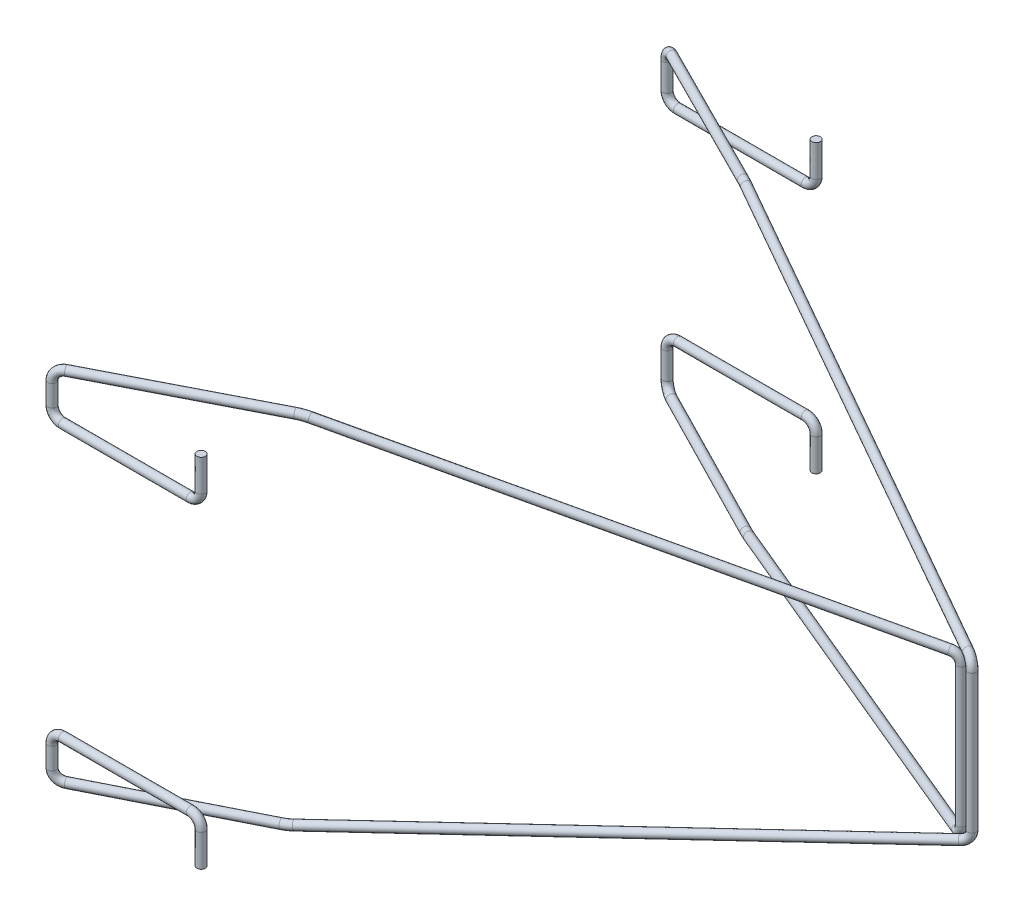
SolidWorks part; units mm, degrees
ref_plane "Front" through (0, 0, 0) normal (0, 0, 1) x (1, 0, 0)
ref_plane "Top" through (0, 0, 0) normal (0, 1, 0) x (1, 0, 0)
ref_plane "Right" through (0, 0, 0) normal (1, 0, 0) x (0, 0, -1)
sketch "Sketch1" plane through (0, 0, 0) normal (1, 0, 0) x (0, 0, -1)
  line L0 (105.8477, -16.8339) -> (302.3227, -5.6613)
  line L1 (0, 17) -> (100, 17)
  line L2 (0, 17) -> (0, -17)
  line L3 (0, -17) -> (100, -17)
  line L4 (105.8477, 16.8339) -> (302.3227, 5.6613)
  line L5 (308, 5.5) -> (360, 5.5)
  line L6 (308, -5.5) -> (360, -5.5)
  line L7 (360, -5.5) -> (360, 5.5)
  line L8 (360, 0) -> (0, 0) construction
  line L9 (116.1325, 16.249) -> (116.1325, -16.249) construction
  line L10 (173.8675, 12.9659) -> (173.8675, -12.9659) construction
  line L11 (145, 14.6075) -> (145, -14.6075) construction
  line L12 (145, 0) -> (173.8675, -50) construction
  line L13 (145, 0) -> (116.1325, -50) construction
  line L14 (116.1325, -50) -> (173.8675, -50) construction
  line L15 (145, -50) -> (145, -14.6075) construction
  arc A0 (100, 17) -> (105.8477, 16.8339) centre (100, -86) cw
  arc A1 (100, -17) -> (105.8477, -16.8339) centre (100, 86) ccw
  arc A2 (302.3227, 5.6613) -> (308, 5.5) centre (308, 105.5) ccw
  arc A3 (302.3227, -5.6613) -> (308, -5.5) centre (308, -105.5) cw
  dimension "D5" = 103
  dimension "D6" = 100
  dimension "D1" = 11
  dimension "D2" = 34
  dimension "D3" = 100
  dimension "D4" = 360
  dimension "D7" = 52
  dimension "D8" = 145
  dimension "D9" = 50
ref_plane "Plane1" through (0, 0, -145) normal (0, 0, 1) x (1, 0, 0)
ref_plane "Plane2" through (0, 0, -116.1325) normal (0, 0, 1) x (1, 0, 0)
ref_plane "Plane3" through (0, 0, -173.8675) normal (0, 0, 1) x (1, 0, 0)
sketch "Sketch2" plane through (0, 0, -145) normal (0, 0, 1) x (1, 0, 0)
  line L0 (0, 0) -> (50, 0) construction
  line L1 (49.5, -6.5) -> (50.5, 6.5) construction
  line L2 (50.5, 6.5) -> (49.5, 6.5) construction
  line L3 (50.5, 6.5) -> (50.5, -6.5) construction
  line L4 (50.5, -6.5) -> (49.5, -6.5) construction
  line L5 (49.5, 6.5) -> (49.5, -6.5) construction
  line L6 (50, 0) -> (50, 6) construction
  dimension "D1" = 1
  dimension "D2" = 13
  dimension "D3" = 50
  dimension "D4" = 12
sketch "Sketch3" plane through (0, 0, -116.1325) normal (0, 0, 1) x (1, 0, 0)
  line L0 (6, 12.749) -> (-6, 12.749)
  line L1 (7, 13.749) -> (7, 16.749)
  line L2 (-7, 13.749) -> (-7, 15.749)
  line L3 (0, 12.749) -> (0, 16.249) construction
  line L4 (0, 16.249) -> (0, 12.749) construction
  arc A0 (6, 12.749) -> (7, 13.749) centre (6, 13.749) ccw
  arc A1 (-6, 12.749) -> (-7, 13.749) centre (-6, 13.749) cw
  dimension "D2" = 1
  dimension "D1" = 3
  dimension "D3" = 3.5
  dimension "D4" = 2
  dimension "D5" = 12
sketch "Sketch4" plane through (0, 0, -173.8675) normal (0, 0, 1) x (1, 0, 0)
  line L0 (6, 9.4659) -> (-6, 9.4659)
  line L1 (7, 10.4659) -> (7, 13.4659)
  line L2 (-7, 10.4659) -> (-7, 12.9659)
  line L3 (7, 13.749) -> (7, 16.749) construction
  line L5 (0, 9.4659) -> (0, 12.9659) construction
  arc A0 (-6, 9.4659) -> (-7, 10.4659) centre (-6, 10.4659) cw
  arc A1 (6, 9.4659) -> (7, 10.4659) centre (6, 10.4659) ccw
  arc A2 (6, 12.749) -> (7, 13.749) centre (6, 13.749) ccw construction
  arc A3 (-7, 13.749) -> (-6, 12.749) centre (-6, 13.749) ccw construction
  dimension "D1" = 2.5
  dimension "D2" = 3.5
sketch "Sketch5" plane through (0, 0, -116.1325) normal (0, 0, 1) x (1, 0, 0)
  line L0 (6, -12.749) -> (-6, -12.749)
  line L1 (7, -13.749) -> (7, -16.749)
  line L2 (-7, -13.749) -> (-7, -15.749)
  line L3 (0, -12.749) -> (0, -16.249) construction
  line L4 (0, 12.749) -> (0, 16.249) construction
  line L5 (6, 12.749) -> (-6, 12.749) construction
  line L6 (7, 13.749) -> (7, 16.749) construction
  line L7 (-7, 13.749) -> (-7, 15.749) construction
  arc A0 (-6, -12.749) -> (-7, -13.749) centre (-6, -13.749) ccw
  arc A1 (6, -12.749) -> (7, -13.749) centre (6, -13.749) cw
  arc A2 (6, 12.749) -> (7, 13.749) centre (6, 13.749) ccw construction
  arc A3 (-7, 13.749) -> (-6, 12.749) centre (-6, 13.749) ccw construction
sketch "Sketch6" plane through (0, 0, -173.8675) normal (0, 0, 1) x (1, 0, 0)
  line L0 (6, -9.4659) -> (-6, -9.4659)
  line L1 (0, -9.4659) -> (0, -12.9659) construction
  line L2 (7, -10.4659) -> (7, -13.4659)
  line L3 (-7, -10.4659) -> (-7, -12.9659)
  line L6 (0, 9.4659) -> (0, 12.9659) construction
  line L7 (6, 12.749) -> (-6, 12.749) construction
  line L8 (7, 13.749) -> (7, 16.749) construction
  line L9 (-7, 10.4659) -> (-7, 12.9659) construction
  arc A0 (-6, -9.4659) -> (-7, -10.4659) centre (-6, -10.4659) ccw
  arc A1 (6, -9.4659) -> (7, -10.4659) centre (6, -10.4659) cw
  arc A2 (6, 12.749) -> (7, 13.749) centre (6, 13.749) ccw construction
  arc A3 (-7, 13.749) -> (-6, 12.749) centre (-6, 13.749) ccw construction
ref_plane "Plane4" through (-48.5016, 0, -94.9281) normal (-0.455, 0, -0.8905) x (-0.8905, 0, 0.455)
sketch "Sketch7" plane through (-48.5016, 0, -94.9281) normal (-0.455, 0, -0.8905) x (-0.8905, 0, 0.455)
  line L0 (-109.2534, 7.4796) -> (-64.6105, 16.6468)
  line L3 (-63.6048, 16.749) -> (-47.6048, 16.749)
  arc A0 (-47.6048, 16.749) -> (-46.6048, 15.749) centre (-47.6048, 15.749) cw
  arc A1 (-109.2534, 7.4796) -> (-110.0523, 6.5) centre (-109.0523, 6.5) ccw
  arc A2 (-63.6048, 16.749) -> (-64.6105, 16.6468) centre (-63.6048, 11.749) ccw
  dimension "D1" = 1
  dimension "D2" = 5
  dimension "D3" = 16
ref_plane "Plane5" through (68.9955, 0, -135.0392) normal (0.455, 0, -0.8905) x (-0.8905, 0, -0.455)
sketch "Sketch8" plane through (68.9955, 0, -135.0392) normal (0.455, 0, -0.8905) x (-0.8905, 0, -0.455)
  line L0 (21.8927, 6.5) -> (21.8927, -6.5)
  line L1 (22.751, -7.4899) -> (67.6316, -13.9154)
  line L4 (68.3402, -13.9659) -> (84.3402, -13.9659)
  arc A0 (21.8927, -6.5) -> (22.751, -7.4899) centre (22.8927, -6.5) ccw
  arc A1 (84.3402, -13.9659) -> (85.3402, -12.9659) centre (84.3402, -12.9659) ccw
  arc A2 (68.3402, -13.9659) -> (67.6316, -13.9154) centre (68.3402, -8.9659) cw
  dimension "D1" = 1
  dimension "D3" = 5
  dimension "D2" = 16
ref_plane "Plane6" through (0, 6.5, 0) normal (0, 1, 0) x (-1, 0, 0)
sketch "Sketch9" plane through (0, 6.5, 0) normal (0, 1, 0) x (-1, 0, 0)
  circle A0 centre (-49.5, -145) radius 0.4
  dimension "D1" = 0.8
sweep "Sweep1" add profiles "Sketch9" path "Sketch7"
sketch "Sketch10" plane through (0, 15.749, 0) normal (0, -1, 0) x (1, 0, 0)
  circle A1 centre (-7, -116.1325) radius 0.4
  circle A2 centre (-7, -116.1325) radius 0.4
  dimension "D1" = 0
sweep "Sweep2" add profiles "Sketch10" path "Sketch3"
sketch "Sketch11" plane through (0, 6.5, 0) normal (0, -1, 0) x (1, 0, 0)
  circle A1 centre (49.5, -145) radius 0.4
  circle A2 centre (49.5, -145) radius 0.4
  dimension "D1" = 0
sweep "Sweep3" add profiles "Sketch11" path "Sketch8"
sketch "Sketch12" plane through (0, -12.9659, 0) normal (0, 1, 0) x (-1, 0, 0)
  circle A1 centre (7, -173.8675) radius 0.4
  circle A2 centre (7, -173.8675) radius 0.4
  dimension "D1" = 0
sweep "Sweep5" add profiles "Sketch12" path "Sketch6"
ref_plane "Plane7" through (-47.9757, 0, -95.5609) normal (-0.4487, 0, -0.8937) x (-0.8937, 0, 0.4487)
sketch "Sketch13" plane through (-47.9757, 0, -95.5609) normal (-0.4487, 0, -0.8937) x (-0.8937, 0, 0.4487)
  line L0 (-61.8498, -16.749) -> (-46.8498, -16.749)
  line L1 (-62.8162, -16.6547) -> (-109.3827, -7.4811)
  line L2 (-110.1894, -6.5) -> (-110.1894, 6.5)
  arc A0 (-46.8498, -16.749) -> (-45.8498, -15.749) centre (-46.8498, -15.749) ccw
  arc A1 (-61.8498, -16.749) -> (-62.8162, -16.6547) centre (-61.8498, -11.749) cw
  arc A2 (-109.3827, -7.4811) -> (-110.1894, -6.5) centre (-109.1894, -6.5) cw
  dimension "D1" = 1
  dimension "D3" = 5
  dimension "D2" = 15
ref_plane "Plane8" through (68.3079, 0, -136.0597) normal (0.4487, 0, -0.8937) x (-0.8937, 0, -0.4487)
sketch "Sketch14" plane through (68.3079, 0, -136.0597) normal (0.4487, 0, -0.8937) x (-0.8937, 0, -0.4487)
  line L0 (83.2657, 13.9659) -> (68.2657, 13.9659)
  line L1 (67.5852, 13.9194) -> (20.79, 7.4907)
  arc A0 (83.2657, 13.9659) -> (84.2657, 12.9659) centre (83.2657, 12.9659) cw
  arc A1 (68.2657, 13.9659) -> (67.5852, 13.9194) centre (68.2657, 8.9659) ccw
  arc A2 (20.79, 7.4907) -> (19.9261, 6.5) centre (20.9261, 6.5) ccw
  dimension "D1" = 5
  dimension "D3" = 1
  dimension "D2" = 15
sketch "Sketch15" plane through (0, 6.5, 0) normal (0, 1, 0) x (-1, 0, 0)
  circle A0 centre (-50.5, -145) radius 0.4
  circle A1 centre (-49.5, -145) radius 0.4 construction
sweep "Sweep6" add profiles "Sketch15" path "Sketch14"
sketch "Sketch16" plane through (0, 12.9659, 0) normal (0, -1, 0) x (1, 0, 0)
  circle A1 centre (-7, -173.8675) radius 0.4
  circle A2 centre (-7, -173.8675) radius 0.4
  dimension "D1" = 0
sweep "Sweep7" add profiles "Sketch16" path "Sketch4"
sketch "Sketch17" plane through (0, 6.5, 0) normal (0, -1, 0) x (1, 0, 0)
  circle A1 centre (50.5, -145) radius 0.4
  circle A2 centre (50.5, -145) radius 0.4
  dimension "D1" = 0
sweep "Sweep8" add profiles "Sketch17" path "Sketch13"
sketch "Sketch18" plane through (0, -15.749, 0) normal (0, 1, 0) x (-1, 0, 0)
  circle A1 centre (7, -116.1325) radius 0.4
  circle A2 centre (7, -116.1325) radius 0.4
  dimension "D1" = 0
sweep "Sweep9" add profiles "Sketch18" path "Sketch5"
